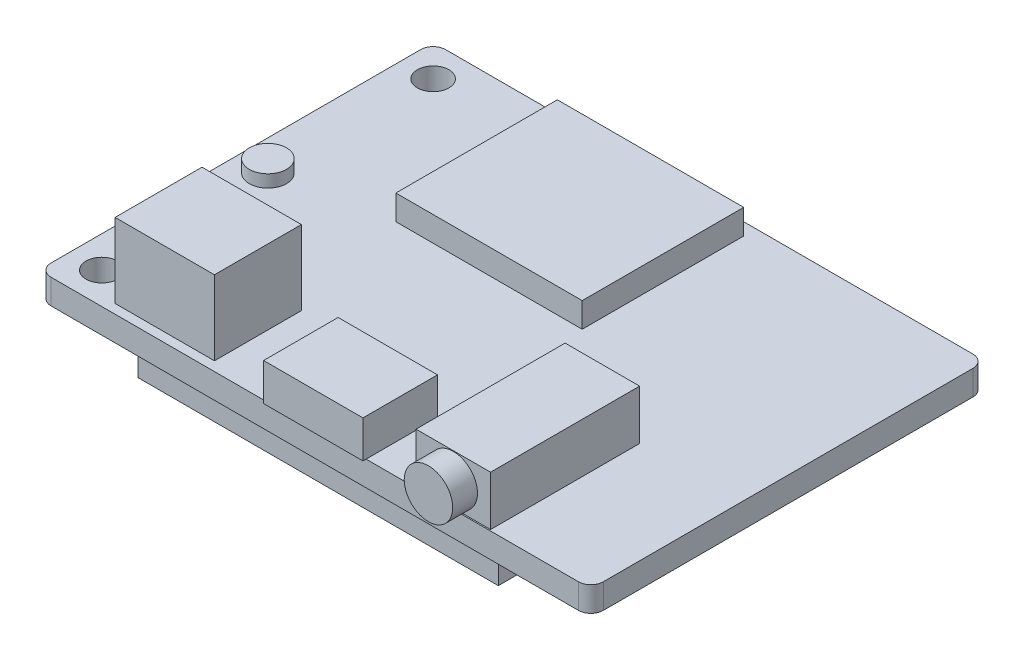
SolidWorks part; units mm, degrees
ref_plane "Front Plane" through (0, 0, 0) normal (0, 0, 1) x (1, 0, 0)
ref_plane "Top Plane" through (0, 0, 0) normal (0, 1, 0) x (1, 0, 0)
ref_plane "Right Plane" through (0, 0, 0) normal (1, 0, 0) x (0, 0, -1)
sketch "Sketch1" plane through (0, 0, 0) normal (0, 1, 0) x (1, 0, 0)
  line L1 (-22.225, 15.875) -> (22.225, 15.875)
  line L2 (-22.225, 15.875) -> (-22.225, -15.875)
  line L3 (-22.225, -15.875) -> (22.225, -15.875)
  line L4 (22.225, 15.875) -> (22.225, -15.875)
  line L5 (-22.225, 15.875) -> (22.225, -15.875) construction
  line L6 (-22.225, -15.875) -> (22.225, 15.875) construction
  point P0 (0, 0)
  dimension "D1" = 44.45
  dimension "D2" = 31.75
extrude "Boss-Extrude1" add sketch "Sketch1" along normal blind 2
sketch "Sketch2" plane through (0, 2, 0) normal (0, 1, 0) x (1, 0, 0)
  line L0 (-22.225, 15.875) -> (-22.225, -15.875) construction
  line L1 (-22.225, -15.875) -> (22.225, -15.875) construction
  line L2 (22.225, 15.875) -> (-22.225, 15.875) construction
  circle A0 centre (-19.685, -13.335) radius 1.27
  circle A1 centre (-19.685, 13.335) radius 1.27
  dimension "D1" = 2.54
  dimension "D4" = 2.54
  dimension "D2" = 2.54
  dimension "D3" = 2.54
  dimension "D5" = 26.67
  dimension "D6" = 2.54
extrude "Cut-Extrude1" cut sketch "Sketch2" against normal blind 2
fillet "Fillet1" radius 1 1 edges at (-22.225, 1, -15.875)
fillet "Fillet2" radius 1 1 edges at (-22.225, 1, 15.875)
fillet "Fillet3" radius 1 1 edges at (22.225, 1, -15.875)
fillet "Fillet4" radius 1 1 edges at (22.225, 1, 15.875)
sketch "Sketch3" plane through (0, 2, 0) normal (0, 1, 0) x (1, 0, 0)
  line L0 (22.225, -14.875) -> (22.225, 14.875) construction
  line L1 (-16.827, -15.125) -> (-8.827, -15.125)
  line L2 (-16.827, -15.125) -> (-16.827, -8.125)
  line L3 (-16.827, -8.125) -> (-8.827, -8.125)
  line L4 (-8.827, -15.125) -> (-8.827, -8.125)
  line L5 (-16.827, -15.125) -> (-8.827, -8.125) construction
  line L6 (-16.827, -8.125) -> (-8.827, -15.125) construction
  line L7 (21.225, 15.875) -> (-21.225, 15.875) construction
  point P0 (-12.827, -11.625)
  dimension "D1" = 7
  dimension "D2" = 8
  dimension "D3" = 35.052
  dimension "D4" = 24
extrude "Boss-Extrude2" add sketch "Sketch3" along normal blind 6
sketch "Sketch4" plane through (0, 2, 0) normal (0, 1, 0) x (1, 0, 0)
  line L0 (21.225, 15.875) -> (-21.225, 15.875) construction
  line L1 (-3.873, -10.125) -> (4.127, -10.125)
  line L2 (-3.873, -10.125) -> (-3.873, -16.125)
  line L3 (-3.873, -16.125) -> (4.127, -16.125)
  line L4 (4.127, -10.125) -> (4.127, -16.125)
  line L5 (-3.873, -10.125) -> (4.127, -16.125) construction
  line L6 (-3.873, -16.125) -> (4.127, -10.125) construction
  line L7 (22.225, -14.875) -> (22.225, 14.875) construction
  point P0 (0.127, -13.125)
  dimension "D1" = 8
  dimension "D2" = 6
  dimension "D3" = 26
  dimension "D4" = 22.098
extrude "Boss-Extrude3" add sketch "Sketch4" along normal blind 3
sketch "Sketch5" plane through (0, 2, 0) normal (0, 1, 0) x (1, 0, 0)
  line L0 (4.127, -15.875) -> (21.225, -15.875) construction
  line L1 (8.049, -3.775) -> (14.049, -3.775)
  line L2 (8.049, -3.775) -> (8.049, -15.775)
  line L3 (8.049, -15.775) -> (14.049, -15.775)
  line L4 (14.049, -3.775) -> (14.049, -15.775)
  line L5 (8.049, -3.775) -> (14.049, -15.775) construction
  line L6 (8.049, -15.775) -> (14.049, -3.775) construction
  line L7 (22.225, -14.875) -> (22.225, 14.875) construction
  point P0 (11.049, -9.775)
  dimension "D1" = 12
  dimension "D2" = 6
  dimension "D3" = 0.1
  dimension "D4" = 11.176
extrude "Boss-Extrude4" add sketch "Sketch5" along normal blind 4
sketch "Sketch6" plane through (0, 0, 15.775) normal (0, 0, 1) x (1, 0, 0)
  line L0 (8.049, 6) -> (8.049, 2) construction
  line L1 (4.127, 2) -> (21.225, 2) construction
  circle A0 centre (11.049, 4) radius 1.95
  dimension "D1" = 3.9
  dimension "D3" = 2
  dimension "D2" = 3
extrude "Boss-Extrude5" add sketch "Sketch6" along normal blind 2
sketch "Sketch7" plane through (0, 2, 0) normal (0, 1, 0) x (1, 0, 0)
  line L0 (-21.225, -15.875) -> (-3.873, -15.875) construction
  line L1 (22.225, -14.875) -> (22.225, 14.875) construction
  circle A0 centre (-19.775, 0.125) radius 1.5
  dimension "D1" = 3
  dimension "D2" = 16
  dimension "D3" = 42
extrude "Boss-Extrude6" add sketch "Sketch7" along normal blind 1
sketch "Sketch9" plane through (0, 2, 0) normal (0, 1, 0) x (1, 0, 0)
  line L0 (21.225, 15.875) -> (-21.225, 15.875) construction
  line L1 (3.775, 1.875) -> (-11.225, 1.875)
  line L2 (3.775, 1.875) -> (3.775, 14.875)
  line L3 (3.775, 14.875) -> (-11.225, 14.875)
  line L4 (-11.225, 1.875) -> (-11.225, 14.875)
  line L5 (3.775, 1.875) -> (-11.225, 14.875) construction
  line L6 (3.775, 14.875) -> (-11.225, 1.875) construction
  line L7 (-22.225, 14.875) -> (-22.225, -14.875) construction
  point P0 (-3.725, 8.375)
  dimension "D1" = 15
  dimension "D2" = 13
  dimension "D3" = 1
  dimension "D4" = 11
extrude "Boss-Extrude7" add sketch "Sketch9" along normal blind 2
sketch "Sketch10" plane through (0, 0, 0) normal (0, -1, 0) x (1, 0, 0)
  line L0 (-22.225, -14.875) -> (-22.225, 14.875) construction
  line L1 (-15.225, -2.125) -> (13.775, -2.125)
  line L2 (-15.225, -2.125) -> (-15.225, 14.875)
  line L3 (-15.225, 14.875) -> (13.775, 14.875)
  line L4 (13.775, -2.125) -> (13.775, 14.875)
  line L5 (-15.225, -2.125) -> (13.775, 14.875) construction
  line L6 (-15.225, 14.875) -> (13.775, -2.125) construction
  line L7 (-21.225, 15.875) -> (21.225, 15.875) construction
  point P0 (-0.725, 6.375)
  dimension "D1" = 17
  dimension "D2" = 29
  dimension "D3" = 7
  dimension "D4" = 1
extrude "Boss-Extrude8" add sketch "Sketch10" along normal blind 2.5
